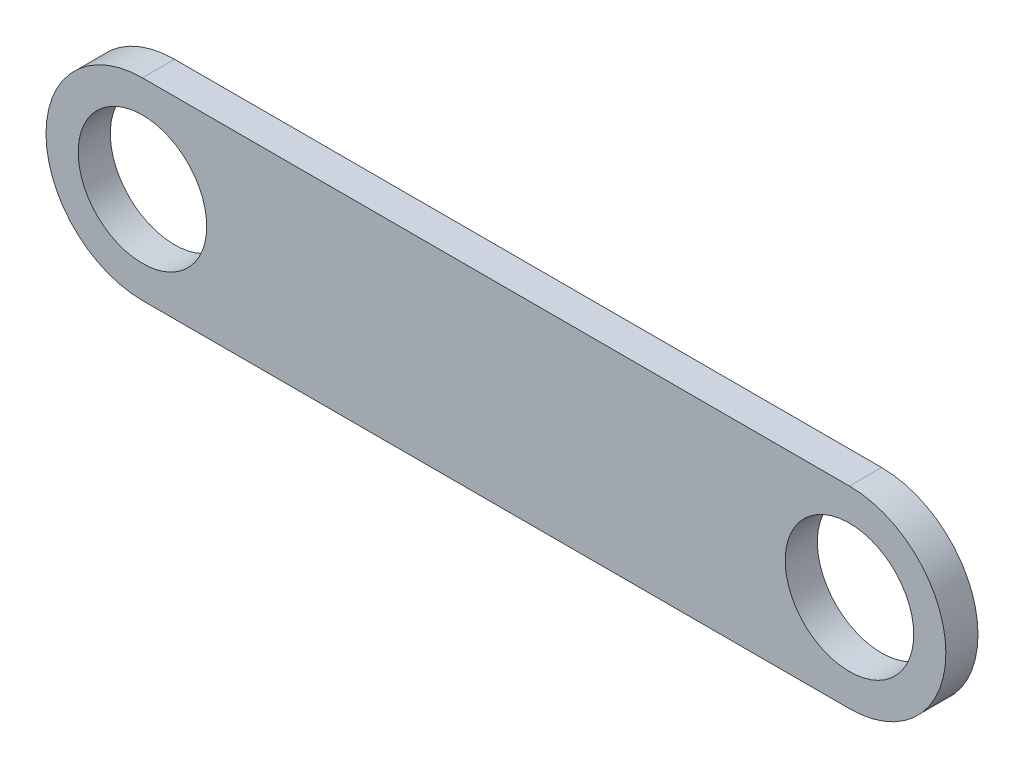
SolidWorks part; units mm, degrees
ref_plane "Alzado" through (0, 0, 0) normal (0, 0, 1) x (1, 0, 0)
ref_plane "Planta" through (0, 0, 0) normal (0, 1, 0) x (1, 0, 0)
ref_plane "Vista lateral" through (0, 0, 0) normal (1, 0, 0) x (0, 0, -1)
sketch "Croquis1" plane through (0, 0, 0) normal (0, 0, 1) x (1, 0, 0)
  line L1 (-53.125, 17.1875) -> (56.875, 17.1875)
  line L3 (-53.125, -12.8125) -> (56.875, -12.8125)
  arc A0 (-53.125, 17.1875) -> (-53.125, -12.8125) centre (-53.125, 2.1875) ccw
  arc A1 (56.875, -12.8125) -> (56.875, 17.1875) centre (56.875, 2.1875) ccw
  circle A2 centre (-53.125, 2.1875) radius 10
  circle A3 centre (56.875, 2.1875) radius 10
  dimension "D3" = 20
  dimension "D4" = 20
  dimension "D1" = 110
  dimension "D2" = 30
extrude "Saliente-Extruir1" add sketch "Croquis1" along normal blind 5
